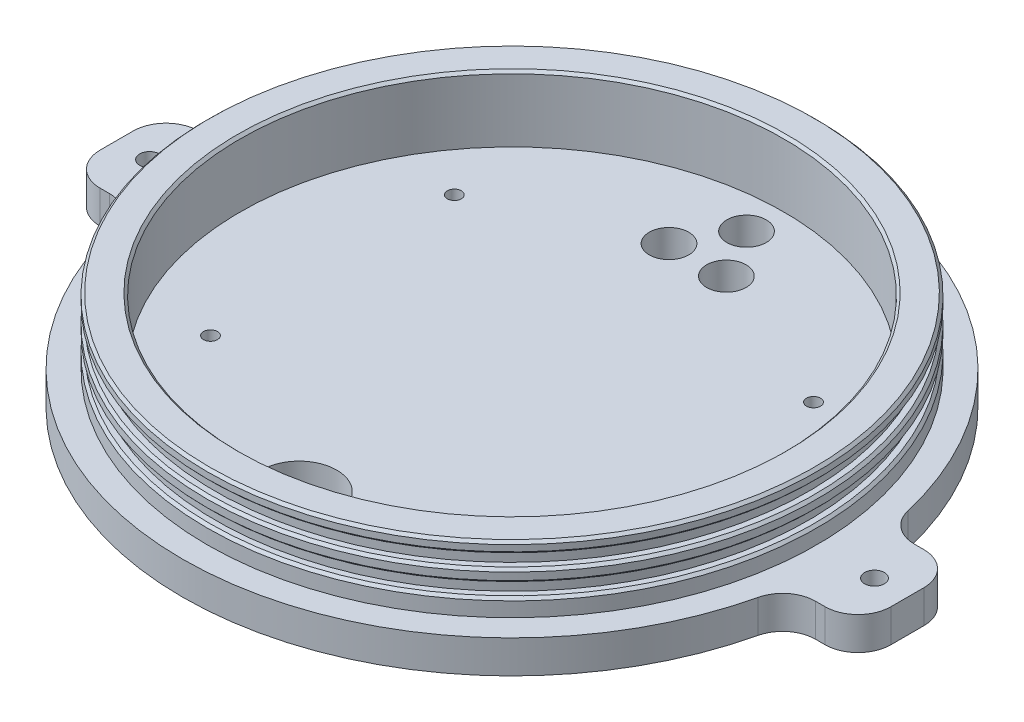
SolidWorks part; units mm, degrees
material "6061 Alloy"
ref_plane "Front Plane" through (0, 0, 0) normal (0, 0, 1) x (1, 0, 0)
ref_plane "Top Plane" through (0, 0, 0) normal (0, 1, 0) x (1, 0, 0)
ref_plane "Right Plane" through (0, 0, 0) normal (1, 0, 0) x (0, 0, -1)
sketch "Sketch1" plane through (0, 0, 0) normal (0, 1, 0) x (1, 0, 0)
  circle A0 centre (0, 0) radius 63.5
extrude "Extrude1" add sketch "Sketch1" along normal blind 6.35
sketch "Sketch2" plane through (0, 6.35, 0) normal (0, 1, 0) x (-1, 0, 0)
  circle A0 centre (0, 0) radius 58.7375
  circle A1 centre (0, 0) radius 52.3875
extrude "Extrude2" add sketch "Sketch2" along normal blind 12.7
sketch "Sketch3" plane through (0, 0, 0) normal (1, 0, 0) x (0, 0, -1)
  line L0 (-58.7375, 19.05) -> (-58.7375, 6.35) construction
  line L1 (-58.7375, 16.8472) -> (-57.15, 16.8472)
  line L2 (-58.7375, 16.8472) -> (-58.7375, 14.4659)
  line L3 (-58.7375, 14.4659) -> (-57.15, 14.4659)
  line L4 (-57.15, 16.8472) -> (-57.15, 14.4659)
  line L5 (0, 0) -> (0, 23.3452) construction
  line L6 (-58.7375, 12.033) -> (-57.15, 12.033)
  line L7 (-58.7375, 12.033) -> (-58.7375, 9.6518)
  line L8 (-58.7375, 9.6518) -> (-57.15, 9.6518)
  line L9 (-57.15, 12.033) -> (-57.15, 9.6518)
  dimension "D1" = 1.5875
  dimension "D2" = 2.3812
revolve "Cut-Revolve1" cut sketch "Sketch3" angle 360 about L5
chamfer "Chamfer1" distance 0.5 angle 45 6 edges at (0, 9.6518, -58.7375) (0, 12.033, -58.7375) (0, 14.4659, -58.7375) (0, 16.8472, -58.7375) (0, 19.05, 58.7375) (0, 19.05, 52.3875)
sketch "Sketch5" plane through (0, 0, 0) normal (0, -1, 0) x (1, 0, 0)
  line L1 (-69.85, 9.525) -> (69.85, 9.525)
  line L2 (-76.2, 3.175) -> (-76.2, -3.175)
  line L3 (-69.85, -9.525) -> (69.85, -9.525)
  line L4 (76.2, 3.175) -> (76.2, -3.175)
  arc A0 (-69.85, 9.525) -> (-76.2, 3.175) centre (-69.85, 3.175) ccw
  arc A1 (-69.85, -9.525) -> (-76.2, -3.175) centre (-69.85, -3.175) cw
  arc A2 (76.2, -3.175) -> (69.85, -9.525) centre (69.85, -3.175) cw
  arc A3 (76.2, 3.175) -> (69.85, 9.525) centre (69.85, 3.175) ccw
  point P7 (-76.2, 9.525)
  point P10 (-76.2, -9.525)
  point P15 (76.2, 9.525)
  dimension "D5" = 6.35
  dimension "D1" = 152.4
  dimension "D2" = 76.2
  dimension "D3" = 19.05
  dimension "D4" = 9.525
extrude "Extrude3" add sketch "Sketch5" against normal up to surface (6.35 mm away) up to face at (0, 6.35, 52.3875)
sketch "Sketch4" plane through (0, 0, 0) normal (0, -1, 0) x (1, 0, 0)
  circle A0 centre (-5.7837, -36.0388) radius 3.8
  circle A1 centre (-0.3826, -45.5779) radius 3.8
  circle A2 centre (5.1779, -36.1309) radius 3.8
  circle A3 centre (0, 0) radius 36.5 construction
  dimension "D1" = 10.962
  dimension "D2" = 73
  dimension "D3" = 10.962
  dimension "D4" = 10.962
extrude "Cut-Extrude1" cut sketch "Sketch4" against normal blind 12.7
hole_wizard "#6 Clearance Hole1" positions "3DSketch1" profile "Sketch6" hole size "#6" standard "Ansi Inch"
sketch3d "3DSketch1"
  line L0 (-62.7816, 0, 9.525) -> (-69.85, 0, 9.525) construction
  line L1 (69.85, 0, 9.525) -> (62.7816, 0, 9.525) construction
  line L4 (76.2, 0, -3.175) -> (76.2, 0, 3.175) construction
  line L5 (-76.2, 0, 3.175) -> (-76.2, 0, -3.175) construction
  point P0 (-69.85, 0, 0)
  point P2 (69.85, 0, 0)
  dimension "D1" = 9.525
  dimension "D2" = 9.525
  dimension "D3" = 6.35
  dimension "D4" = 6.35
sketch "Sketch6" plane through (-69.85, 0, 0) normal (1, 0, 0) x (0, 0, -1)
  line L0 (0, 0) -> (0, 331.3408)
  line L1 (0, 331.3408) -> (1.8986, 330.2)
  line L2 (1.8986, 330.2) -> (1.8986, 0)
  line L5 (1.8986, 0) -> (0, 0)
  line L10 (0, 331.3408) -> (-1.8987, 330.2) construction
  line L11 (0, -6.35) -> (0, 107.95) construction
  dimension "Hole Dia." = 3.7973
  dimension "Hole Depth" = 330.2
  dimension "Drill Angle" = 118
fillet "Fillet1" radius 6.35 4 edges at (-62.7816, 3.175, 9.525) (62.7816, 3.175, 9.525) (62.7816, 3.175, -9.525) (-62.7816, 3.175, -9.525)
hole_wizard "M14.5 (14.5) Diameter Hole1" positions "3DSketch3" profile "Sketch8" hole size "M14.5" standard "Ansi Metric" end condition through all
sketch3d "3DSketch3"
  point P0 (0, 0, 41.0207)
sketch "Sketch8" plane through (0, 0, 41.0207) normal (1, 0, 0) x (0, 0, -1)
  line L0 (0, 0) -> (0, 19.05)
  line L1 (0, 19.05) -> (7.25, 19.05)
  line L2 (7.25, 19.05) -> (7.25, 0)
  line L5 (7.25, 0) -> (0, 0)
  line L11 (0, -6.35) -> (0, 107.95) construction
  dimension "Thru Hole Dia." = 14.5
  dimension "Thru Hole Depth" = 19.05
hole_wizard "Tap Drill for #6 Tap1" positions "3DSketch4" profile "Sketch9" hole size "#6-32" standard "Ansi Inch"
sketch3d "3DSketch4"
  line L0 (-30.3553, 0, 0) -> (30.3553, 0, 0) construction
  line L2 (0, 0, -16.5724) -> (0, 0, 22.3152) construction
  line L5 (-34.6075, 6.35, -23.495) -> (-34.6075, 6.35, 23.495) construction
  line L6 (-34.6075, 6.35, 23.495) -> (34.6075, 6.35, 23.495) construction
  line L7 (34.6075, 6.35, 23.495) -> (34.6075, 6.35, -23.495) construction
  line L8 (34.6075, 6.35, -23.495) -> (-34.6075, 6.35, -23.495) construction
  line L10 (0, 6.35, -23.495) -> (0, 6.35, 23.495) construction
  line L12 (34.6075, 6.35, 0) -> (-34.6075, 6.35, 0) construction
  line L13 (0, 0, 0) -> (0, 6.35, 0) construction
  point P0 (-34.6075, 6.35, -23.495)
  point P2 (-34.6075, 6.35, 23.495)
  point P4 (34.6075, 6.35, 23.495)
  point P6 (34.6075, 6.35, -23.495)
  dimension "D1" = 69.215
  dimension "D2" = 46.99
sketch "Sketch9" plane through (-34.6075, 6.35, -23.495) normal (1, 0, 0) x (0, 0, 1)
  line L0 (0, 0) -> (0, 4.1147)
  line L1 (0, 4.1147) -> (1.3525, 3.302)
  line L2 (1.3525, 3.302) -> (1.3525, 0)
  line L5 (1.3525, 0) -> (0, 0)
  line L10 (0, 4.1147) -> (-1.3526, 3.302) construction
  line L11 (0, -6.35) -> (0, 107.95) construction
  dimension "Hole Dia." = 2.7051
  dimension "Hole Depth" = 3.302
  dimension "Drill Angle" = 118
